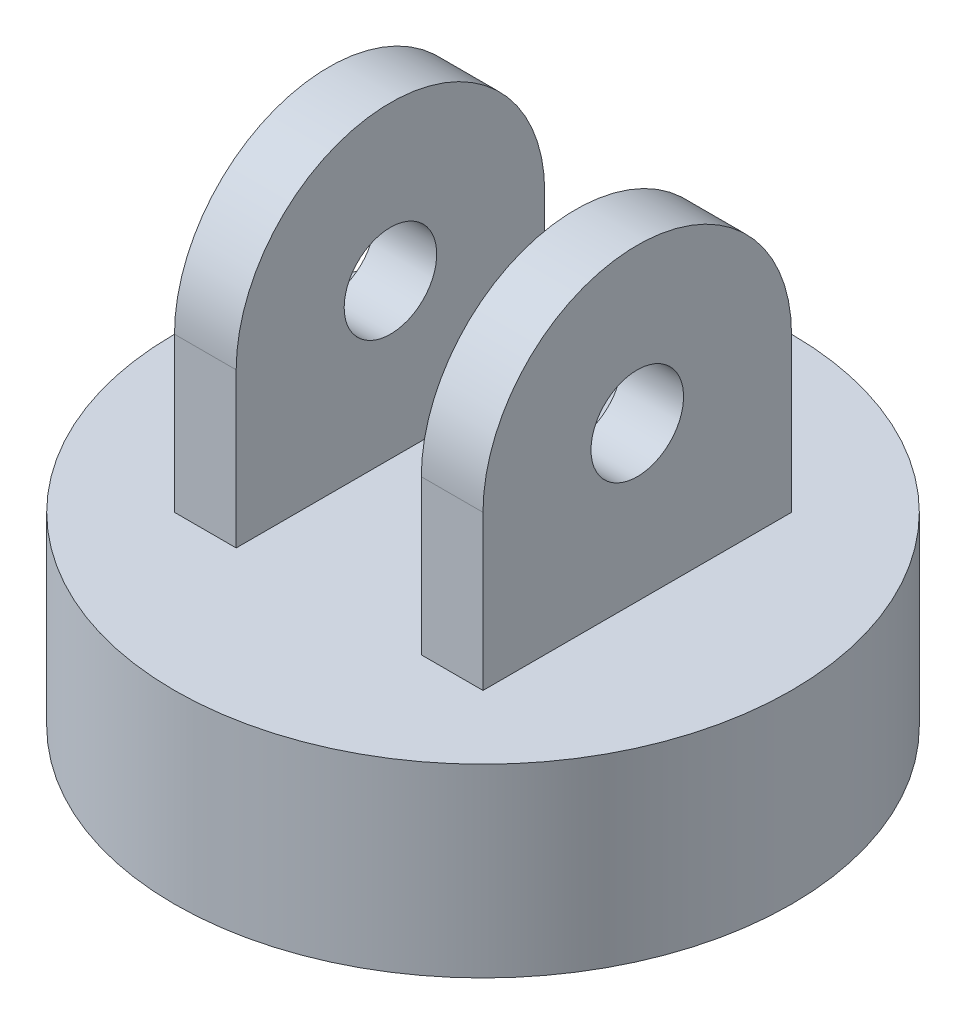
SolidWorks part; units mm, degrees
ref_plane "Front Plane" through (0, 0, 0) normal (0, 0, 1) x (1, 0, 0)
ref_plane "Top Plane" through (0, 0, 0) normal (0, 1, 0) x (1, 0, 0)
ref_plane "Right Plane" through (0, 0, 0) normal (1, 0, 0) x (0, 0, -1)
sketch "Sketch1" plane through (0, 0, 0) normal (0, 1, 0) x (1, 0, 0)
  circle A0 centre (0, 0) radius 50
  dimension "D1" = 100
extrude "Boss-Extrude1" add sketch "Sketch1" along normal blind 30
sketch "Sketch2" plane through (0, 30, 0) normal (0, 1, 0) x (1, 0, 0)
  line L0 (-15, -25) -> (-15, 25)
  line L2 (-25, -25) -> (-25, 25)
  line L4 (25, -25) -> (25, 25)
  line L5 (-25, -25) -> (25, 25) construction
  line L6 (-25, 25) -> (25, -25) construction
  line L7 (15, -25) -> (15, 25)
  line L8 (-25, 25) -> (-15, 25)
  line L9 (15, 25) -> (25, 25)
  line L10 (25, -25) -> (15, -25)
  line L11 (-15, -25) -> (-25, -25)
  point P0 (0, 0)
  dimension "D1" = 50
  dimension "D2" = 50
  dimension "D3" = 10
  dimension "D4" = 10
extrude "Boss-Extrude2" add sketch "Sketch2" along normal blind 50
sketch "Sketch3" plane through (-25, 0, 0) normal (-1, 0, 0) x (0, 0, 1)
  line L1 (-25, 55) -> (-34.2018, 55)
  line L2 (-34.2018, 55) -> (-34.2018, 88.2545)
  line L3 (-34.2018, 88.2545) -> (30.8527, 88.2545)
  line L4 (30.8527, 88.2545) -> (30.8527, 55)
  line L5 (30.8527, 55) -> (25, 55)
  arc A0 (25, 55) -> (-25, 55) centre (0, 55) ccw
sketch "Sketch4" plane through (-25, 0, 0) normal (-1, 0, 0) x (0, 0, 1)
  line L0 (30.8527, 88.2545) -> (30.8527, 55) construction
  line L1 (30.8527, 55) -> (25, 55) construction
  line L2 (-25, 55) -> (-34.2018, 55) construction
  line L3 (-34.2018, 55) -> (-34.2018, 88.2545) construction
  line L4 (-34.2018, 88.2545) -> (30.8527, 88.2545) construction
  line L5 (30.8527, 88.2545) -> (30.8527, 55)
  line L6 (30.8527, 55) -> (25, 55)
  line L7 (-25, 55) -> (-34.2018, 55)
  line L8 (-34.2018, 55) -> (-34.2018, 88.2545)
  line L9 (-34.2018, 88.2545) -> (30.8527, 88.2545)
  arc A0 (25, 55) -> (-25, 55) centre (0, 55) ccw construction
  arc A1 (25, 55) -> (-25, 55) centre (0, 55) ccw
extrude "Cut-Extrude2" cut sketch "Sketch4" against normal blind 50
sketch "Sketch5" plane through (-25, 0, 0) normal (-1, 0, 0) x (0, 0, 1)
  circle A0 centre (0, 55) radius 7.5
  dimension "D1" = 15
extrude "Cut-Extrude3" cut sketch "Sketch5" against normal blind 50
